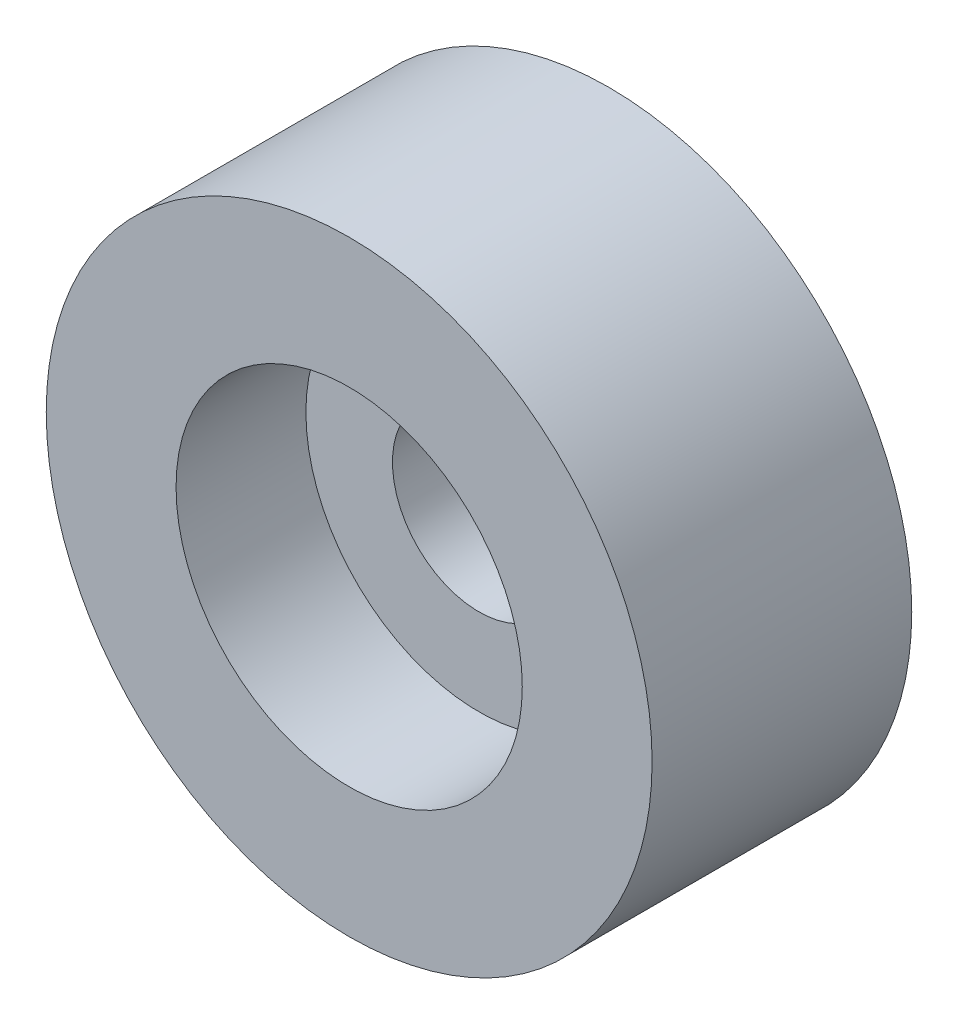
SolidWorks part; units mm, degrees
ref_plane "前视基准面" through (0, 0, 0) normal (0, 0, 1) x (1, 0, 0)
ref_plane "上视基准面" through (0, 0, 0) normal (0, 1, 0) x (1, 0, 0)
ref_plane "右视基准面" through (0, 0, 0) normal (1, 0, 0) x (0, 0, -1)
sketch "草图1" plane through (0, 0, 0) normal (0, 0, 1) x (1, 0, 0)
  circle A0 centre (0, 0) radius 3.5
  circle A1 centre (0, 0) radius 1
  dimension "D1" = 2
  dimension "D2" = 7
extrude "凸台-拉伸1" add sketch "草图1" along normal blind 3
cosmetic thread "装饰螺纹线1" parameters "D2"=6
sketch "草图2" plane through (0, 0, 3) normal (0, 0, 1) x (1, 0, 0)
  circle A0 centre (0, 0) radius 2
  dimension "D1" = 4
extrude "切除-拉伸1" cut sketch "草图2" against normal blind 1.5
